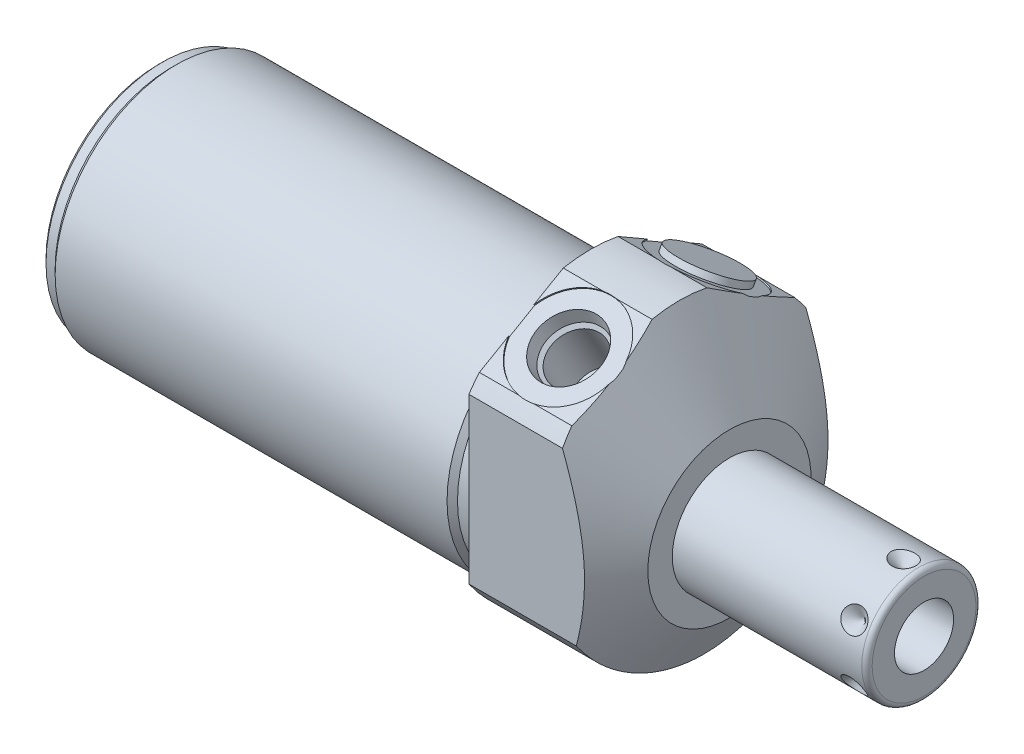
SolidWorks part; units mm, degrees
material "Alloy Steel"
ref_plane "Front Plane" through (0, 0, 0) normal (0, 0, 1) x (1, 0, 0)
ref_plane "Top Plane" through (0, 0, 0) normal (0, 1, 0) x (1, 0, 0)
ref_plane "Right Plane" through (0, 0, 0) normal (1, 0, 0) x (0, 0, -1)
ref_plane "Plane1" through (0, 0, 0) normal (1, 0, 0) x (0, 0, -1)
sketch "Sketch1" plane through (0, 0, 0) normal (1, 0, 0) x (0, 0, -1)
  circle A0 centre (0, 0) radius 28.575
  dimension "D1" = 57.15
extrude "Extrude1" add sketch "Sketch1" along normal blind 27.0002 and the other way blind 84.1248
ref_plane "Plane2" through (0, 0, 0) normal (1, 0, 0) x (0, 0, -1)
sketch "Sketch2" plane through (0, 0, 0) normal (1, 0, 0) x (0, 0, -1)
  line L0 (-25.9842, -4.191) -> (25.9842, -4.191) construction
  circle A0 centre (0, -4.191) radius 23.622
  circle A2 centre (0, 0) radius 28.575
  circle A3 centre (0, 0) radius 28.575
  dimension "D2" = 47.244
  dimension "D1" = 4.191
  dimension "D3" = 0
extrude "Cut-Extrude1" cut sketch "Sketch2" against normal up to next
ref_plane "Plane4" through (0, 0, 0) normal (-1, 0, 0) x (0, 0, 1)
sketch "Sketch4" plane through (0, 0, 0) normal (-1, 0, 0) x (0, 0, 1)
  line L0 (23.6855, -25.6662) -> (23.6855, 17.4761)
  line L1 (23.6855, 17.4761) -> (0, 31.1509)
  line L2 (-23.6855, -25.6662) -> (-23.6855, 17.4761)
  line L3 (-23.6855, 17.4761) -> (0, 31.1509)
  line L4 (0, -31.5613) -> (0, 34.1372) construction
  arc A2 (23.6855, -25.6662) -> (-23.6855, -25.6662) centre (0, 0) ccw
  dimension "D4" = 69.85
  dimension "D1" = 47.371
  dimension "D2" = 30.607
  dimension "D3" = 120
extrude "Cut-Extrude3" cut sketch "Sketch4" against normal up to next
ref_plane "Plane6" through (0, 0, 0) normal (0, 0, 1) x (1, 0, 0)
sketch "Sketch6" plane through (0, 0, 0) normal (0, 0, 1) x (1, 0, 0)
  line L0 (0.7504, 57.15) -> (27.0002, 11.684)
  line L1 (-0.5621, -4.191) -> (28.3127, -4.191) construction
  line L2 (-84.1248, -4.191) -> (0, -4.191) construction
  line L3 (27.0002, 11.684) -> (27.0002, 57.15)
  line L4 (27.0002, 57.15) -> (0.7504, 57.15)
  line L5 (27.0002, 15.9852) -> (27.0002, -15.9852) construction
  dimension "D1" = 60
  dimension "D2" = 31.75
  dimension "D3" = 122.682
revolve "Cut-Revolve2" cut sketch "Sketch6" angle 360 about L1
ref_plane "Plane7" through (9.0932, 23.1369, 13.3727) normal (1, 0, 0) x (0, 0.5, -0.866)
sketch "S2D0002" plane through (9.0932, 23.1369, 13.3727) normal (1, 0, 0) x (0, 0.5, -0.866)
  line L0 (0, 0) -> (6.1849, 0)
  line L1 (6.1849, 0) -> (5.6423, -2.5527)
  line L2 (5.6423, -2.5527) -> (4.9784, -3.2166)
  line L3 (4.9784, -3.2166) -> (4.9784, -13.462)
  line L4 (4.9784, -13.462) -> (0, -13.462)
  line L5 (0, -13.462) -> (0, 0)
  line L6 (0, -14.1351) -> (0, 0.6731) construction
  dimension "D1" = 13.462
revolve "Cut-Revolve3" cut sketch "S2D0002" angle 360 about L6
ref_plane "Plane8" through (9.0932, 23.1369, -13.3727) normal (1, 0, 0) x (0, -0.5, -0.866)
sketch "Sketch8" plane through (9.0932, 23.1369, -13.3727) normal (1, 0, 0) x (0, -0.5, -0.866)
  line L0 (0, 0) -> (6.1849, 0)
  line L1 (6.1849, 0) -> (5.6423, -2.5527)
  line L2 (5.6423, -2.5527) -> (4.9784, -3.2166)
  line L3 (4.9784, -3.2166) -> (4.9784, -13.462)
  line L4 (4.9784, -13.462) -> (0, -13.462)
  line L5 (0, -13.462) -> (0, 0)
  line L6 (0, -14.1351) -> (0, 0.6731) construction
  dimension "D1" = 13.462
revolve "Cut-Revolve4" cut sketch "Sketch8" angle 360 about L6
ref_plane "Plane10" through (0, 0, 0) normal (0, 0, 1) x (1, 0, 0)
sketch "Sketch18" plane through (0, 23.3632, 13.4887) normal (0, 0.866, 0.5) x (1, 0, 0)
  circle A0 centre (9.0932, -0.0127) radius 9.525
  dimension "D1" = 19.05
extrude "Cut-Extrude4" cut sketch "Sketch18" against normal blind 0.254
sketch "Sketch19" plane through (0, 23.3632, -13.4887) normal (0, 0.866, -0.5) x (1, 0, 0)
  circle A0 centre (9.0932, 0.0127) radius 9.525
  circle A1 centre (9.0932, 0.0127) radius 6.1849 construction
  dimension "D1" = 19.05
extrude "Cut-Extrude5" cut sketch "Sketch19" against normal blind 0.254
sketch "Sketch10" plane through (0, 0, 0) normal (0, 0, 1) x (1, 0, 0)
  line L0 (0, 19.431) -> (0, 18.415)
  line L1 (0, 18.415) -> (-3.302, 18.415)
  line L2 (-3.302, 18.415) -> (-4.318, 19.431)
  line L3 (-4.5339, -4.191) -> (0.2159, -4.191) construction
  line L4 (0, 19.431) -> (-4.318, 19.431)
  line L5 (-84.1248, -4.191) -> (0, -4.191) construction
  line L6 (0, 19.431) -> (-84.1248, 19.431) construction
  line L7 (0, 21.9392) -> (0, 18.6529) construction
  dimension "D1" = 45.212
  dimension "D2" = 45
  dimension "D3" = 3.302
revolve "Cut-Revolve6" cut sketch "Sketch10" angle 360 about L3
ref_plane "Plane12" through (0, 0, 0) normal (0, 0, 1) x (1, 0, 0)
sketch "Sketch12" plane through (0, 0, 0) normal (0, 0, 1) x (1, 0, 0)
  line L0 (-84.1248, 19.431) -> (-84.1248, 18.415)
  line L1 (-84.1248, 18.415) -> (-81.5848, 18.415)
  line L2 (-81.5848, 18.415) -> (-80.5688, 19.431)
  line L3 (-84.3026, -4.191) -> (-80.391, -4.191) construction
  line L4 (-84.1248, 19.431) -> (-80.5688, 19.431)
  line L5 (-84.1248, -4.191) -> (-4.318, -4.191) construction
  line L6 (-4.318, 19.431) -> (-84.1248, 19.431) construction
  line L7 (-84.1248, 19.431) -> (-84.1248, -27.813) construction
  dimension "D1" = 45.212
  dimension "D2" = 45
  dimension "D3" = 2.54
revolve "Cut-Revolve8" cut sketch "Sketch12" angle 360 about L3
chamfer "Chamfer1" distance 0.762 angle 45 1 edges at (-84.1248, -4.191, 22.606)
ref_plane "Plane13" through (0, 0, 0) normal (0, 0, 1) x (0, -1, 0)
sketch "Sketch13" plane through (0, 0, 0) normal (0, 0, 1) x (0, -1, 0)
  line L0 (4.191, 27.0002) -> (4.191, 64.8716)
  line L1 (4.191, 64.8716) -> (14.2875, 64.8716)
  line L2 (15.3035, 63.8556) -> (15.3035, 27.0002)
  line L3 (15.3035, 27.0002) -> (4.191, 27.0002)
  line L4 (4.191, 25.1066) -> (4.191, 66.7652) construction
  line L5 (4.191, -80.5688) -> (4.191, -4.318) construction
  line L6 (20.066, 27.0002) -> (-11.684, 27.0002) construction
  line L7 (-18.415, 0) -> (26.797, 0) construction
  arc A0 (15.3035, 63.8556) -> (14.2875, 64.8716) centre (14.2875, 63.8556) ccw
  dimension "D3" = 1.016
  dimension "D1" = 22.225
  dimension "D2" = 64.8716
revolve "Revolve1" add sketch "Sketch13" angle 360 about L4
ref_plane "Plane14" through (64.8716, -9.9441, 0) normal (0, 0, 1) x (0, -1, 0)
sketch "S2D0001" plane through (64.8716, -9.9441, 0) normal (0, 0, 1) x (0, -1, 0)
  line L0 (0, 0) -> (0, -17.018)
  line L1 (0, -17.018) -> (-5.7531, -20.4748)
  line L2 (0, 0) -> (-5.7531, 0)
  line L3 (-5.7531, 0) -> (-5.7531, -20.4748)
  line L4 (-5.7531, -21.4986) -> (-5.7531, 1.0237) construction
  line L5 (-5.7531, -1.016) -> (-5.7531, -37.8714) construction
  line L6 (4.3434, 0) -> (-15.8496, 0) construction
  dimension "D1" = 11.5062
  dimension "D2" = 59
  dimension "D3" = 17.018
revolve "Cut-Revolve9" cut sketch "S2D0001" angle 360 about L4
ref_plane "Plane15" through (27.0002, 23.1432, -13.3617) normal (0, -0.866, 0.5) x (0, -0.5, -0.866)
sketch "Sketch15" plane through (27.0002, 23.1432, -13.3617) normal (0, -0.866, 0.5) x (0, -0.5, -0.866)
  circle A0 centre (0.0127, -17.907) radius 6.9469
  arc A1 (-2.4139, -8.6963) -> (-9.4205, -16.5878) centre (0.0127, -17.907) ccw construction
  dimension "D1" = 13.8938
extrude "Extrude2" add sketch "Sketch15" against normal blind 1.27
ref_plane "Plane16" through (60.9092, -15.3035, 0) normal (0, 0, 1) x (-1, 0, 0)
ref_plane "Plane17" through (0, -3.1433, -1.8148) normal (0, 0.866, 0.5) x (-1, 0, 0)
sketch "Sketch16" plane through (60.9092, 6.9215, 0) normal (0, 0, -1) x (-1, 0, 0)
  line L0 (0, 0) -> (2.413, 0)
  line L1 (2.413, 0) -> (0, -2.413)
  line L2 (0, 0) -> (0, -2.413)
  line L3 (0, -4.4865) -> (0, 0.1207) construction
  line L4 (-3.9624, -1.016) -> (-3.9624, -21.209) construction
  line L5 (33.909, 0) -> (-2.9464, 0) construction
  dimension "D1" = 45
  dimension "D2" = 3.9624
  dimension "D3" = 4.826
revolve "Cut-Revolve10" cut sketch "Sketch16" angle 360 about L3
pattern_circular "CirPattern1" count 6 over 360 about axis through (25.1066, -4.191, 0) along (-1, 0, 0) of "Cut-Revolve10"
